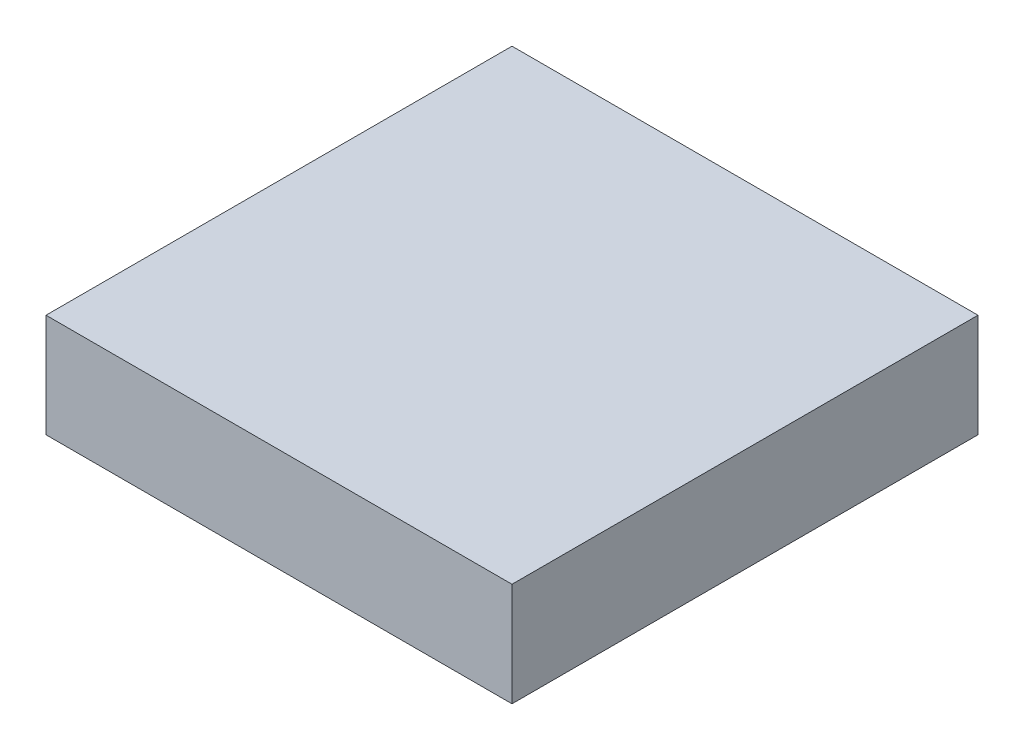
SolidWorks part; units mm, degrees
ref_plane "Front Plane" through (0, 0, 0) normal (0, 0, 1) x (1, 0, 0)
ref_plane "Top Plane" through (0, 0, 0) normal (0, 1, 0) x (1, 0, 0)
ref_plane "Right Plane" through (0, 0, 0) normal (1, 0, 0) x (0, 0, -1)
sketch "Sketch1" plane through (0, 0, 0) normal (0, 1, 0) x (1, 0, 0)
  line L1 (0, 0) -> (-45, 0)
  line L2 (0, 0) -> (0, 45)
  line L3 (0, 45) -> (-45, 45)
  line L4 (-45, 0) -> (-45, 45)
  dimension "D1" = 45
  dimension "D2" = 45
extrude "Extrude1" add sketch "Sketch1" along normal blind 10
